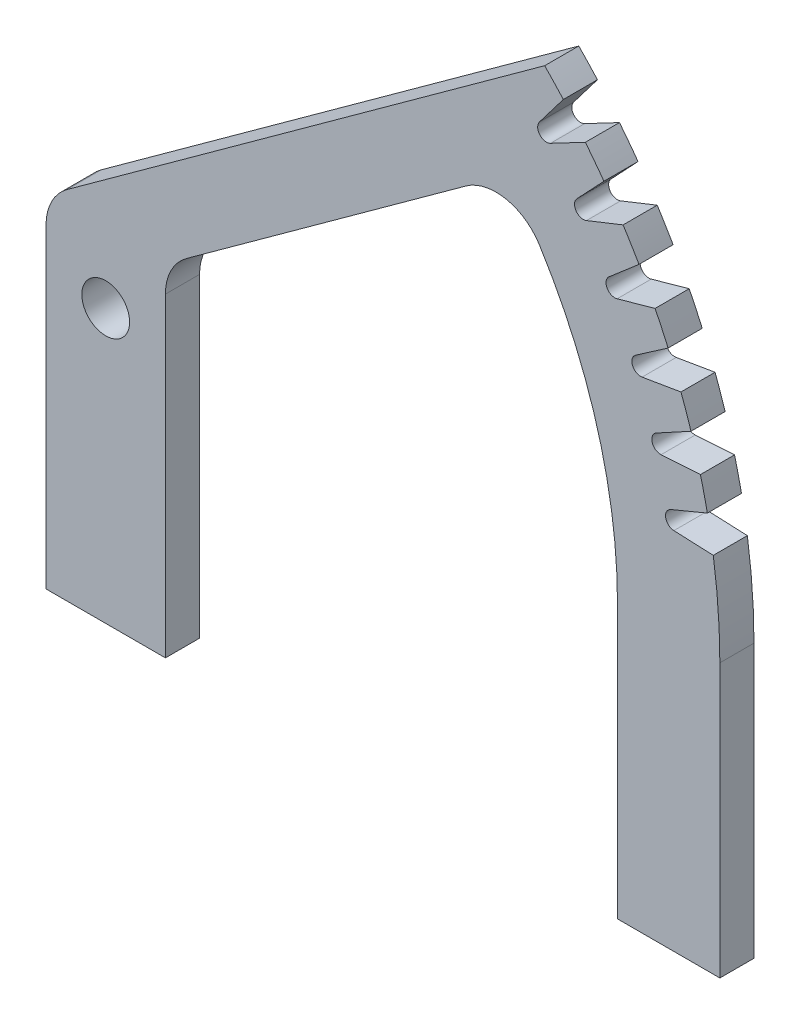
SolidWorks part; units mm, degrees
material "Acier non allié"
ref_plane "Plan de face" through (0, 0, 0) normal (0, 0, 1) x (1, 0, 0)
ref_plane "Plan de dessus" through (0, 0, 0) normal (0, 1, 0) x (1, 0, 0)
ref_plane "Plan de droite" through (0, 0, 0) normal (1, 0, 0) x (0, 0, -1)
sketch "Esquisse1" plane through (0, 0, 0) normal (0, 0, 1) x (1, 0, 0)
  line L0 (-96.202, 152.1354) -> (0, 0) construction
  line L1 (0, 0) -> (180, 0) construction
  line L2 (150, -80) -> (180, -80)
  line L3 (166.5257, 26.8244) -> (178.0652, 26.3206)
  line L4 (165.6574, 31.7484) -> (176.3288, 36.1686)
  line L5 (154.9861, 27.3282) -> (177.2654, 31.2567) construction
  line L6 (162.7723, 44.2213) -> (174.3007, 44.9362)
  line L7 (161.39, 49.0265) -> (171.5362, 54.5465)
  line L8 (157.2067, 61.126) -> (168.5957, 63.0516)
  line L9 (155.3259, 65.7587) -> (164.834, 72.3171)
  line L10 (149.891, 77.3501) -> (161.0136, 80.465)
  line L11 (147.5325, 81.7589) -> (156.2966, 89.2825)
  line L12 (140.9065, 92.713) -> (151.639, 96.9825)
  line L13 (138.0966, 96.8488) -> (146.0192, 105.254)
  line L14 (130.3533, 107.0438) -> (140.5762, 112.4204)
  line L15 (127.1232, 110.8604) -> (134.1161, 120.0537)
  line L16 (0, 0) -> (129.1613, 109.3102) construction
  line L20 (0, 0) -> (0, -80) construction
  line L21 (104.0348, 108.059) -> (128.6497, 125.8939)
  line L22 (150, 0) -> (150, -80)
  line L23 (180, 0) -> (180, -80)
  line L24 (17.5, -80) -> (-17.5, -80)
  line L25 (-17.5, -80) -> (-17.5, 12.3448)
  line L26 (-11.301, 24.4915) -> (104.0348, 108.059)
  line L27 (17.5, -80) -> (17.5, 12.3448)
  line L28 (23.699, 24.4915) -> (105.5952, 83.8301)
  arc A0 (155, 0) -> (-82.8406, 131.0055) centre (0, 0) ccw construction
  arc A1 (150, 0) -> (-80.1684, 126.7795) centre (0, 0) ccw construction
  arc A2 (178.0652, 26.3206) -> (176.3288, 36.1686) centre (0, 0) ccw
  arc A3 (162.7723, 44.2213) -> (161.39, 49.0265) centre (162.6138, 46.7771) cw
  arc A4 (176.3288, 36.1686) -> (174.3007, 44.9362) centre (0, 0) ccw
  arc A5 (180, 0) -> (178.0652, 26.3206) centre (0, 0) ccw
  arc A6 (180, 0) -> (-96.202, 152.1354) centre (0, 0) ccw construction
  arc A7 (166.5257, 26.8244) -> (165.6574, 31.7484) centre (166.6374, 29.3827) cw
  arc A8 (171.5362, 54.5465) -> (168.5957, 63.0516) centre (0, 0) ccw
  arc A9 (157.2067, 61.126) -> (155.3259, 65.7587) centre (156.7798, 63.6508) cw
  arc A10 (164.834, 72.3171) -> (161.0136, 80.465) centre (0, 0) ccw
  arc A11 (149.891, 77.3501) -> (147.5325, 81.7589) centre (149.2004, 79.8159) cw
  arc A12 (156.2966, 89.2825) -> (151.639, 96.9825) centre (0, 0) ccw
  arc A13 (140.9065, 92.713) -> (138.0966, 96.8488) centre (139.96, 95.0924) cw
  arc A14 (146.0192, 105.254) -> (140.5762, 112.4204) centre (0, 0) ccw
  arc A15 (130.3533, 107.0438) -> (127.1232, 110.8604) centre (129.1613, 109.3102) cw
  arc A16 (134.1161, 120.0537) -> (128.6497, 125.8939) centre (0, 0) ccw
  circle A21 centre (0, 0) radius 7
  arc A22 (105.5952, 83.8301) -> (127.1069, 79.6482) centre (114.3962, 71.6834) cw
  arc A23 (-17.5, 12.3448) -> (-11.301, 24.4915) centre (-2.5, 12.3448) cw
  arc A24 (17.5, 12.3448) -> (23.699, 24.4915) centre (32.5, 12.3448) cw
  arc A25 (150, 0) -> (127.1069, 79.6482) centre (0, 0) ccw
  point P65 (-17.5, 20)
  point P68 (17.5, 20)
  point P73 (0, 0)
  dimension "D1" = 180
  dimension "D2" = 30
  dimension "D3" = 25
  dimension "D4" = 25
  dimension "D5" = 14
  dimension "D6" = 5
  dimension "D10" = 80
  dimension "D11" = 20
  dimension "D14" = 10
  dimension "D15" = 15
  dimension "D7" = 10
  dimension "D8" = 9
  dimension "D12" = 35
  dimension "D13" = 8
  dimension "D16" = 150
  dimension "D17" = 40.241
  dimension "D9" = 6
extrude "Boss.-Extru.2" add sketch "Esquisse1" along normal mid plane 10
